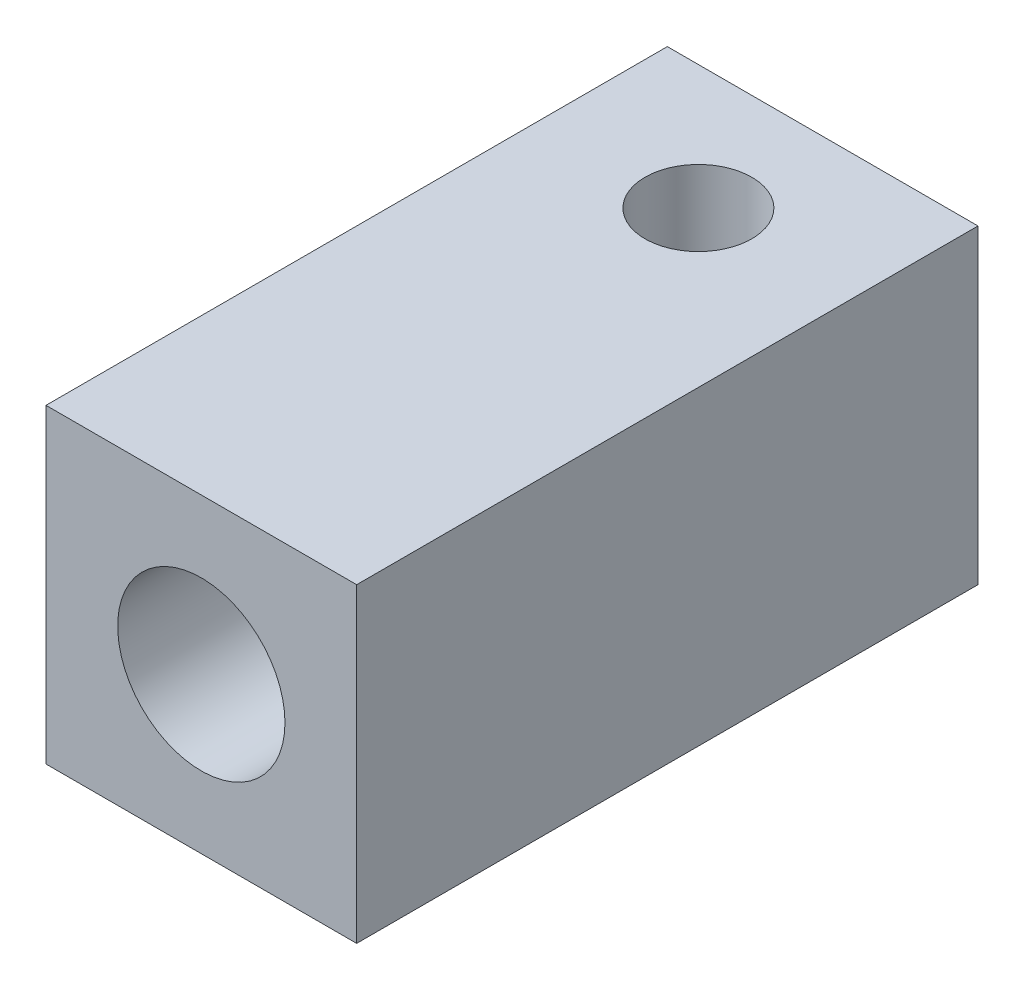
SolidWorks part; units mm, degrees
ref_plane "Front Plane" through (0, 0, 0) normal (0, 0, 1) x (1, 0, 0)
ref_plane "Top Plane" through (0, 0, 0) normal (0, 1, 0) x (1, 0, 0)
ref_plane "Right Plane" through (0, 0, 0) normal (1, 0, 0) x (0, 0, -1)
sketch "Sketch1" plane through (0, 0, 0) normal (0, 0, 1) x (1, 0, 0)
  line L1 (-8.413, 4.7391) -> (-0.913, 4.7391)
  line L2 (-8.413, 4.7391) -> (-8.413, -2.7609)
  line L3 (-8.413, -2.7609) -> (-0.913, -2.7609)
  line L4 (-0.913, 4.7391) -> (-0.913, -2.7609)
  dimension "D1" = 7.5
extrude "Boss-Extrude1" add sketch "Sketch1" along normal blind 15
sketch "10-32 hole for luer screw" plane through (0, 0, 15) normal (0, 0, 1) x (1, 0, 0)
  line L0 (-8.413, 4.7391) -> (-0.913, -2.7609) construction
  circle A0 centre (-4.663, 0.9891) radius 2.0193
  point P4 (-4.663, 0.9891)
  dimension "D1" = 4.0386
sketch "hole for tubing" plane through (0, 0, 0) normal (0, 0, -1) x (-1, 0, 0)
  line L0 (0.913, 4.7391) -> (8.413, -2.7609) construction
  circle A0 centre (4.663, 0.9891) radius 1.1
  point P4 (4.663, 0.9891)
  dimension "D1" = 2.2
extrude "Cut-Extrude1" cut sketch "hole for tubing" against normal through all
extrude "Cut-Extrude2" cut sketch "10-32 hole for luer screw" against normal blind 7.5
sketch "5-40 set screw hole" plane through (0, 4.7391, 0) normal (0, 1, 0) x (1, 0, 0)
  line L0 (-0.913, 0) -> (-8.413, -6) construction
  line L1 (-8.413, -15) -> (-8.413, 0) construction
  circle A0 centre (-4.663, -3) radius 1.2891
  dimension "D2" = 2.5781
  dimension "D1" = 6
extrude "Cut-Extrude3" cut sketch "5-40 set screw hole" against normal blind 2
sketch "Sketch2" plane through (0, 0, 0) normal (0, 0, -1) x (-1, 0, 0)
  line L0 (0.913, -2.7609) -> (8.413, 4.7391) construction
  line L1 (2.7185, -0.9554) -> (6.6076, -0.9554)
  line L2 (2.7185, -0.9554) -> (2.7185, 2.9337)
  line L3 (2.7185, 2.9337) -> (6.6076, 2.9337)
  line L4 (6.6076, -0.9554) -> (6.6076, 2.9337)
  line L5 (6.6076, -0.9554) -> (2.7185, 2.9337) construction
  line L7 (0, -3.9595) -> (7.0377, -3.9595)
  line L8 (0, -3.9595) -> (0, 4.2272)
  line L9 (0, 4.2272) -> (7.0377, 4.2272)
  line L10 (7.0377, -3.9595) -> (7.0377, 4.2272)
  point P8 (4.663, 0.9891)
  point P9 (4.663, 0.9891)
  dimension "D1" = 5.5
extrude "Cut-Extrude4" [suppressed] cut sketch "Sketch2" against normal blind 5
